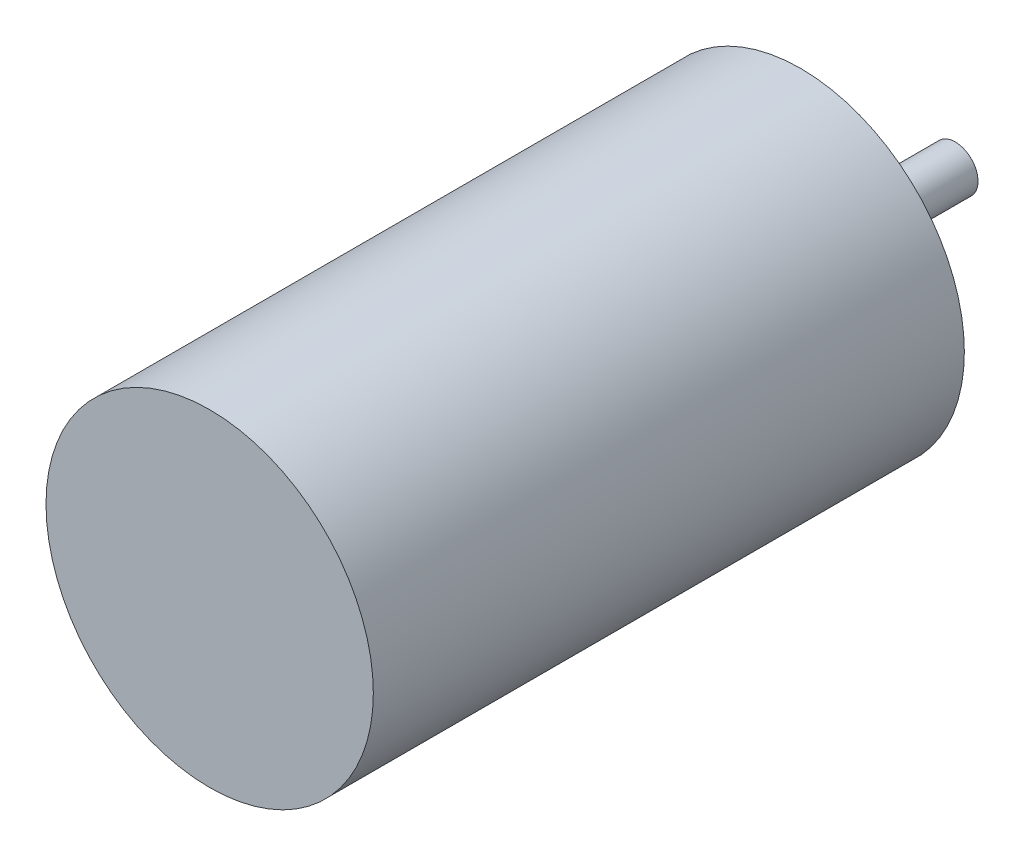
SolidWorks part; units mm, degrees
ref_plane "Front Plane" through (0, 0, 0) normal (0, 0, 1) x (1, 0, 0)
ref_plane "Top Plane" through (0, 0, 0) normal (0, 1, 0) x (1, 0, 0)
ref_plane "Right Plane" through (0, 0, 0) normal (1, 0, 0) x (0, 0, -1)
sketch "Sketch1" plane through (0, 0, 0) normal (0, 0, 1) x (1, 0, 0)
  circle A0 centre (0, 0) radius 18
  dimension "D1" = 36
extrude "Boss-Extrude1" add sketch "Sketch1" along normal blind 65
sketch "Sketch2" plane through (0, 0, 0) normal (0, 0, -1) x (-1, 0, 0)
  circle A0 centre (0, 0) radius 2.5
  dimension "D1" = 5
extrude "Boss-Extrude2" add sketch "Sketch2" along normal blind 17
